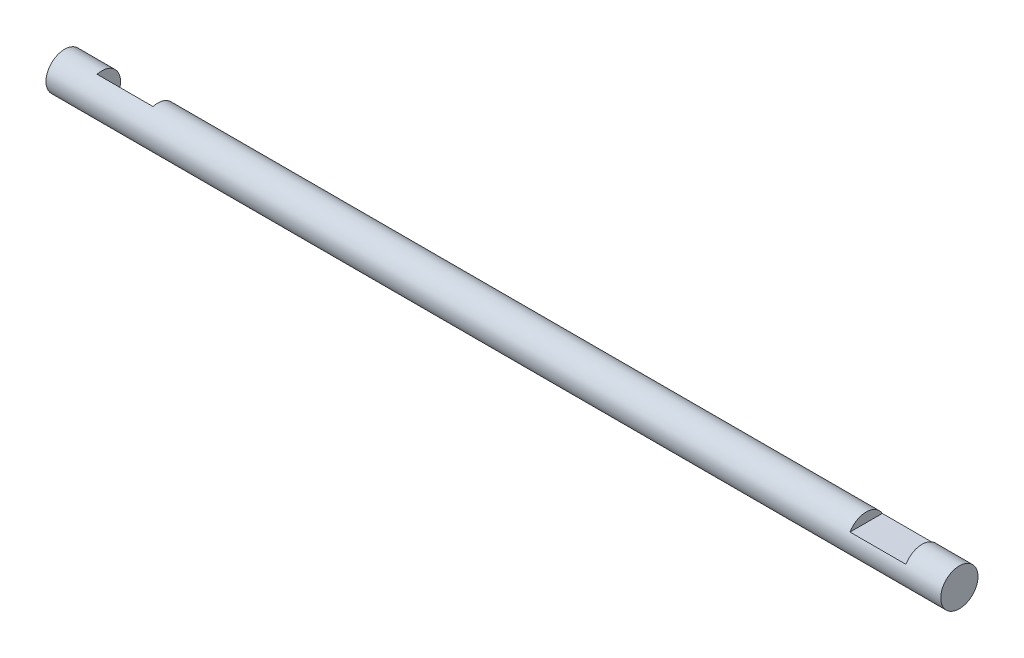
SolidWorks part; units mm, degrees
material "Copper"
ref_plane "Front Plane" through (0, 0, 0) normal (0, 0, 1) x (1, 0, 0)
ref_plane "Top Plane" through (0, 0, 0) normal (0, 1, 0) x (1, 0, 0)
ref_plane "Right Plane" through (0, 0, 0) normal (1, 0, 0) x (0, 0, -1)
sketch "Sketch1" plane through (0, 0, 0) normal (1, 0, 0) x (0, 0, -1)
  circle A0 centre (0, 0) radius 6.35
  dimension "D1" = 12.7
extrude "Boss-Extrude1" add sketch "Sketch1" along normal mid plane 304.8
ref_plane "Plane1" through (0, 6.35, 0) normal (0, 1, 0) x (1, 0, 0)
sketch "Sketch3" plane through (0, 6.35, 0) normal (0, 1, 0) x (1, 0, 0)
  line L0 (-152.4, -6.35) -> (152.4, -6.35) construction
  line L1 (139.7, 6.35) -> (120.65, 6.35)
  line L2 (120.65, 6.35) -> (120.65, -6.35)
  line L3 (120.65, -6.35) -> (139.7, -6.35)
  line L4 (139.7, -6.35) -> (139.7, 6.35)
  line L6 (139.7, 6.35) -> (152.4, 6.35) construction
  line L7 (152.4, 6.35) -> (152.4, -6.35) construction
  line L9 (152.4, -6.35) -> (152.4, 6.35) construction
  line L17 (-152.4, 6.35) -> (-152.4, -6.35) construction
  line L18 (-152.4, 6.35) -> (-152.4, -6.35) construction
  dimension "D1" = 12.7
  dimension "D2" = 19.05
  dimension "D3" = 12.7
extrude "Cut-Extrude1" cut sketch "Sketch3" against normal blind 3.175
ref_plane "Plane3" through (0, 0, 0) normal (0, -0.7071, 0.7071) x (1, 0, 0)
ref_plane "Plane2" through (0, 4.4901, -4.4901) normal (0, -0.7071, 0.7071) x (1, 0, 0)
sketch "Sketch4" plane through (0, 4.4901, -4.4901) normal (0, -0.7071, 0.7071) x (1, 0, 0)
  line L0 (-152.4, -6.35) -> (-152.4, 6.35) construction
  line L1 (-152.4, 6.35) -> (-139.7, 6.35) construction
  line L2 (-152.4, -6.35) -> (152.4, -6.35) construction
  line L3 (-120.65, -6.35) -> (-139.7, -6.35)
  line L4 (-120.65, -6.35) -> (-120.65, 6.35)
  line L5 (-120.65, 6.35) -> (-139.7, 6.35)
  line L6 (-139.7, -6.35) -> (-139.7, 6.35)
  line L7 (-120.65, -6.35) -> (-139.7, 6.35) construction
  line L8 (-120.65, 6.35) -> (-139.7, -6.35) construction
  line L10 (120.65, 6.35) -> (-152.4, 6.35) construction
  line L12 (-152.4, 6.35) -> (-152.4, -6.35) construction
  line L13 (-152.4, -6.35) -> (152.4, -6.35) construction
  line L15 (120.65, 6.1336) -> (139.7, 6.1336) construction
  point P2 (-130.175, 0)
  point P17 (-152.4, 0)
  dimension "D1" = 12.7
extrude "Cut-Extrude2" cut sketch "Sketch4" along normal blind 3.175
